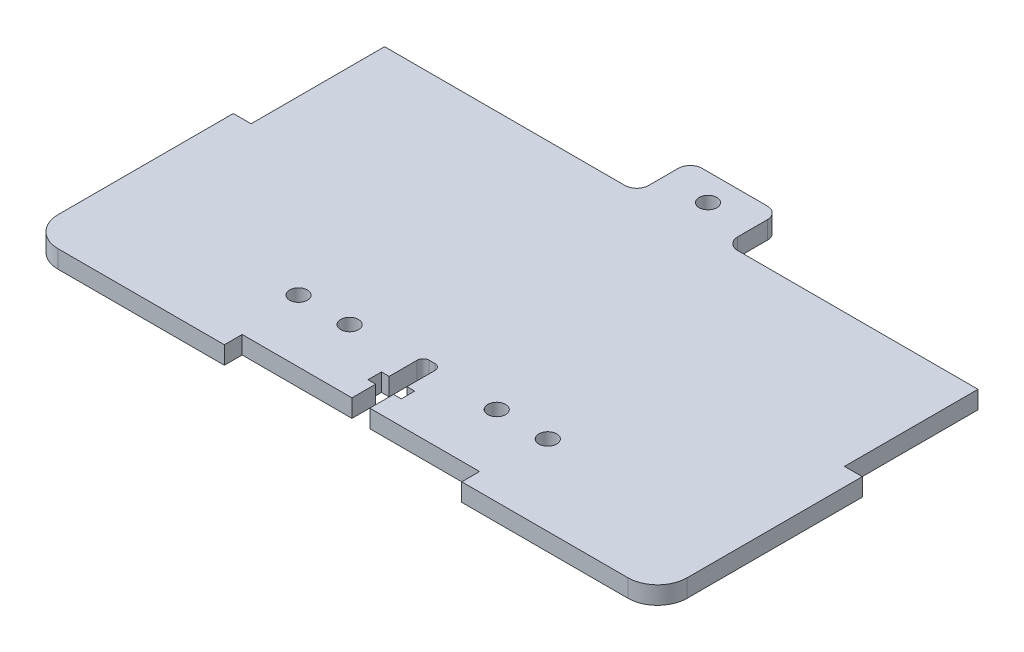
SolidWorks part; units mm, degrees
material "Acrylic (Medium-high impact)"
ref_plane "Plano frontal" through (0, 0, 0) normal (0, 0, 1) x (1, 0, 0)
ref_plane "Plano superior" through (0, 0, 0) normal (0, 1, 0) x (1, 0, 0)
ref_plane "Plano direito" through (0, 0, 0) normal (1, 0, 0) x (0, 0, -1)
sketch "Sketch1" plane through (0, 0, 0) normal (0, 1, 0) x (1, 0, 0)
  line L1 (-53, 28.5) -> (53, 28.5)
  line L2 (-53, 28.5) -> (-53, -28.5)
  line L3 (-53, -28.5) -> (53, -28.5)
  line L4 (53, 28.5) -> (53, -28.5)
  point P4 (0, 28.5)
  point P6 (-53, 0)
  dimension "D1" = 57
  dimension "D2" = 106
extrude "Boss-Extrude1" add sketch "Sketch1" along normal mid plane 3
sketch "Sketch2" plane through (0, 0, 0) normal (0, 1, 0) x (1, 0, 0)
  line L0 (0, -1.65) -> (0, 1.65) construction
  line L1 (-53, 28.5) -> (-50, 28.5)
  line L2 (-53, 28.5) -> (-53, 6)
  line L3 (-53, 6) -> (-50, 6)
  line L4 (-50, 28.5) -> (-50, 6)
  line L5 (50, 28.5) -> (50, 6)
  line L6 (53, 6) -> (50, 6)
  line L7 (53, 28.5) -> (53, 6)
  line L8 (53, 28.5) -> (50, 28.5)
  line L9 (-53, -28.5) -> (53, -28.5) construction
  line L10 (-20, -28.5) -> (20, -28.5)
  line L11 (-20, -28.5) -> (-20, -25.5)
  line L12 (-20, -25.5) -> (20, -25.5)
  line L13 (20, -28.5) -> (20, -25.5)
  point P17 (0, -25.5)
  dimension "D1" = 3
  dimension "D2" = 22.5
  dimension "D3" = 3
  dimension "D4" = 40
extrude "Cut-Extrude1" cut sketch "Sketch2" against normal through all both and the other way through all
sketch "Sketch4" plane through (0, 0, 0) normal (0, 1, 0) x (1, 0, 0)
  line L0 (50, 28.5) -> (-50, 28.5) construction
  line L1 (-7.5, 28.5) -> (7.5, 28.5)
  line L2 (-7.5, 28.5) -> (-7.5, 37.5)
  line L3 (-7.5, 37.5) -> (7.5, 37.5)
  line L4 (7.5, 28.5) -> (7.5, 37.5)
  point P6 (0, 28.5)
  dimension "D1" = 15
  dimension "D2" = 9
extrude "Boss-Extrude2" add sketch "Sketch4" along normal mid plane 3
fillet "Fillet1" radius 2 4 edges at (7.5, 0, -37.5) (-7.5, 0, -37.5) (7.5, 0, -28.5) (-7.5, 0, -28.5)
sketch "Sketch3" plane through (0, 0, 0) normal (0, 1, 0) x (1, 0, 0)
  line L0 (20, -25.5) -> (-20, -25.5) construction
  line L1 (-1.5, -25.5) -> (1.5, -25.5)
  line L2 (-1.5, -25.5) -> (-1.5, -21.5)
  line L3 (-0.5, -13.5) -> (0.5, -13.5)
  line L4 (1.5, -25.5) -> (1.5, -21.5)
  line L5 (1.5, -19.23) -> (2.8, -19.23)
  line L6 (-2.8, -19.23) -> (-1.5, -19.23)
  line L7 (-2.8, -19.23) -> (-2.8, -21.5)
  line L8 (-2.8, -21.5) -> (-1.5, -21.5)
  line L9 (2.8, -19.23) -> (2.8, -21.5)
  line L10 (-1.5, -19.23) -> (-1.5, -14.5)
  line L11 (1.5, -21.5) -> (2.8, -21.5)
  line L12 (1.5, -19.23) -> (1.5, -14.5)
  arc A0 (0.5, -13.5) -> (1.5, -14.5) centre (0.5, -14.5) cw
  arc A1 (-1.5, -14.5) -> (-0.5, -13.5) centre (-0.5, -14.5) cw
  point P6 (0, -13.5)
  dimension "D7" = 1
  dimension "D1" = 3
  dimension "D2" = 2.27
  dimension "D3" = 1.3
  dimension "D4" = 1.3
  dimension "D5" = 4
  dimension "D6" = 12
extrude "Cut-Extrude2" cut sketch "Sketch3" against normal through all both and the other way through all
sketch "Sketch5" plane through (0, 0, 0) normal (0, 1, 0) x (1, 0, 0)
  line L0 (-9.5, 28.5) -> (-50, 28.5) construction
  circle A0 centre (0, 33) radius 1.5
  dimension "D1" = 3
  dimension "D2" = 4.5
extrude "Cut-Extrude3" cut sketch "Sketch5" against normal through all both and the other way through all
fillet "Fillet2" radius 5 2 edges at (53, 0, 28.5) (-53, 0, 28.5)
sketch "Sketch6" plane through (0, 0, 0) normal (0, 1, 0) x (1, 0, 0)
  line L1 (0, -1.65) -> (0, 1.65) construction
  line L2 (-1.5, -25.5) -> (-20, -25.5) construction
  line L4 (-50, 6) -> (-50, -28.0826) construction
  line L6 (-2.8, -21.5) -> (-2.8, -25.5) construction
  line L7 (-21, -15) -> (-12.4, -15) construction
  circle A0 centre (-21, -15) radius 1.5
  circle A1 centre (-12.4, -15) radius 1.5
  circle A2 centre (12.4, -15) radius 1.5
  circle A3 centre (21, -15) radius 1.5
  arc A4 (-53, -23.5) -> (-48, -28.5) centre (-48, -23.5) ccw construction
  point P4 (-16.7, -15)
  dimension "D1" = 3
  dimension "D2" = 8.6
  dimension "D3" = 10.5
  dimension "D4" = 17.2
  dimension "D5" = 29
  dimension "D6" = 13.9
extrude "Cut-Extrude4" cut sketch "Sketch6" against normal through all both and the other way through all
